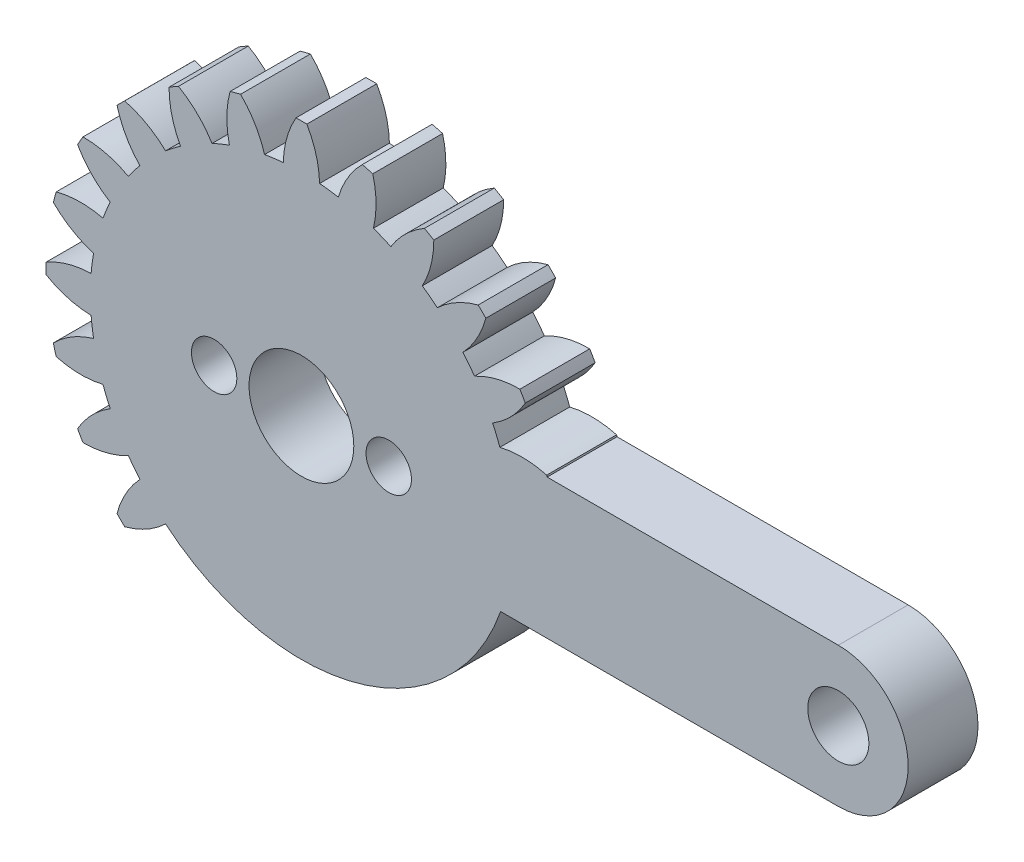
SolidWorks part; units mm, degrees
ref_plane "Front Plane" through (0, 0, 0) normal (0, 0, 1) x (1, 0, 0)
ref_plane "Top Plane" through (0, 0, 0) normal (0, 1, 0) x (1, 0, 0)
ref_plane "Right Plane" through (0, 0, 0) normal (1, 0, 0) x (0, 0, -1)
sketch "Sketch1" plane through (0, 0, 0) normal (0, 0, 1) x (1, 0, 0)
  line L0 (0, 0) -> (0, 14.63) construction
  line L1 (0, 0) -> (30.75, 0) construction
  line L3 (30.75, 4) -> (11.4091, 4)
  line L4 (30.75, -4) -> (11.4091, -4)
  circle A0 centre (0, 0) radius 14.63
  circle A1 centre (0, 0) radius 12.09
  circle A2 centre (0, 0) radius 3
  arc A3 (0.31, 14.6267) -> (1.04, 12.0452) centre (-4.3584, 11.9126) cw
  arc A4 (-0.31, 14.6267) -> (-1.04, 12.0452) centre (4.3584, 11.9126) ccw
  arc A5 (4.0851, 14.0481) -> (4.1221, 11.3656) centre (-1.1267, 12.6347) cw
  arc A6 (3.4862, 14.2086) -> (2.113, 11.9039) centre (7.2931, 10.3787) ccw
  arc A7 (7.5818, 12.5121) -> (6.9233, 9.9114) centre (2.1819, 12.4958) cw
  arc A8 (7.0449, 12.8221) -> (5.1219, 10.9514) centre (9.7308, 8.1374) ccw
  arc A9 (10.5619, 10.1234) -> (9.2526, 7.7818) centre (5.3417, 11.5053) cw
  arc A10 (10.1234, 10.5619) -> (7.7818, 9.2526) centre (11.5053, 5.3417) ccw
  arc A11 (12.8221, 7.0449) -> (10.9514, 5.1219) centre (8.1374, 9.7308) cw
  arc A12 (12.5121, 7.5818) -> (9.9114, 6.9233) centre (12.4958, 2.1819) ccw
  arc A13 (14.2086, 3.4862) -> (11.9039, 2.113) centre (10.3787, 7.2931) cw
  arc A14 (14.0481, 4.0851) -> (11.3656, 4.1221) centre (12.6347, -1.1267) ccw
  arc A15 (14.6267, -0.31) -> (12.0452, -1.04) centre (11.9126, 4.3584) cw
  arc A16 (14.6267, 0.31) -> (12.0452, 1.04) centre (11.9126, -4.3584) ccw
  arc A17 (14.0481, -4.0851) -> (11.3656, -4.1221) centre (12.6347, 1.1267) cw
  arc A18 (14.2086, -3.4862) -> (11.9039, -2.113) centre (10.3787, -7.2931) ccw
  arc A19 (12.5121, -7.5818) -> (9.9114, -6.9233) centre (12.4958, -2.1819) cw
  arc A20 (12.8221, -7.0449) -> (10.9514, -5.1219) centre (8.1374, -9.7308) ccw
  arc A21 (10.1234, -10.5619) -> (7.7818, -9.2526) centre (11.5053, -5.3417) cw
  arc A22 (10.5619, -10.1234) -> (9.2526, -7.7818) centre (5.3417, -11.5053) ccw
  arc A23 (7.0449, -12.8221) -> (5.1219, -10.9514) centre (9.7308, -8.1374) cw
  arc A24 (7.5818, -12.5121) -> (6.9233, -9.9114) centre (2.1819, -12.4958) ccw
  arc A25 (3.4862, -14.2086) -> (2.113, -11.9039) centre (7.2931, -10.3787) cw
  arc A26 (4.0851, -14.0481) -> (4.1221, -11.3656) centre (-1.1267, -12.6347) ccw
  arc A27 (-0.31, -14.6267) -> (-1.04, -12.0452) centre (4.3584, -11.9126) cw
  arc A28 (0.31, -14.6267) -> (1.04, -12.0452) centre (-4.3584, -11.9126) ccw
  arc A29 (-4.0851, -14.0481) -> (-4.1221, -11.3656) centre (1.1267, -12.6347) cw
  arc A30 (-3.4862, -14.2086) -> (-2.113, -11.9039) centre (-7.2931, -10.3787) ccw
  arc A31 (-7.5818, -12.5121) -> (-6.9233, -9.9114) centre (-2.1819, -12.4958) cw
  arc A32 (-7.0449, -12.8221) -> (-5.1219, -10.9514) centre (-9.7308, -8.1374) ccw
  arc A33 (-10.5619, -10.1234) -> (-9.2526, -7.7818) centre (-5.3417, -11.5053) cw
  arc A34 (-10.1234, -10.5619) -> (-7.7818, -9.2526) centre (-11.5053, -5.3417) ccw
  arc A35 (-12.8221, -7.0449) -> (-10.9514, -5.1219) centre (-8.1374, -9.7308) cw
  arc A36 (-12.5121, -7.5818) -> (-9.9114, -6.9233) centre (-12.4958, -2.1819) ccw
  arc A37 (-14.2086, -3.4862) -> (-11.9039, -2.113) centre (-10.3787, -7.2931) cw
  arc A38 (-14.0481, -4.0851) -> (-11.3656, -4.1221) centre (-12.6347, 1.1267) ccw
  arc A39 (-14.6267, 0.31) -> (-12.0452, 1.04) centre (-11.9126, -4.3584) cw
  arc A40 (-14.6267, -0.31) -> (-12.0452, -1.04) centre (-11.9126, 4.3584) ccw
  arc A41 (-14.0481, 4.0851) -> (-11.3656, 4.1221) centre (-12.6347, -1.1267) cw
  arc A42 (-14.2086, 3.4862) -> (-11.9039, 2.113) centre (-10.3787, 7.2931) ccw
  arc A43 (-12.5121, 7.5818) -> (-9.9114, 6.9233) centre (-12.4958, 2.1819) cw
  arc A44 (-12.8221, 7.0449) -> (-10.9514, 5.1219) centre (-8.1374, 9.7308) ccw
  arc A45 (-10.1234, 10.5619) -> (-7.7818, 9.2526) centre (-11.5053, 5.3417) cw
  arc A46 (-10.5619, 10.1234) -> (-9.2526, 7.7818) centre (-5.3417, 11.5053) ccw
  arc A47 (-7.0449, 12.8221) -> (-5.1219, 10.9514) centre (-9.7308, 8.1374) cw
  arc A48 (-7.5818, 12.5121) -> (-6.9233, 9.9114) centre (-2.1819, 12.4958) ccw
  arc A49 (-3.4862, 14.2086) -> (-2.113, 11.9039) centre (-7.2931, 10.3787) cw
  arc A50 (-4.0851, 14.0481) -> (-4.1221, 11.3656) centre (1.1267, 12.6347) ccw
  arc A51 (30.75, 4) -> (30.75, -4) centre (30.75, 0) cw
  circle A52 centre (30.75, 0) radius 1.75
  point P152 (0, 0)
  dimension "D1" = 6
  dimension "D2" = 24.18
  dimension "D3" = 29.26
  dimension "D6" = 5.4
  dimension "D10" = 4
  dimension "D11" = 3.5
  dimension "D4" = 0.62
  dimension "D5" = 2.08
  dimension "D8" = 30.75
  dimension "D9" = 4
  dimension "D12" = 1.0822
  dimension "D7" = 24
extrude "Boss-Extrude3" add sketch "Sketch1" along normal blind 4 contours A1 | A51 L3 A0 L4 A52 | A13 A0 L3 A1 | A16 A0 A13 A1 | A0 A16 A1 A15 | A18 A0 A15 A1 | A0 A18 A1 L4 | A0 A14 A1 L3 | A0 A12 A1 A11 | A0 A10 A1 A9 | A0 A8 A1 A7 | A0 A6 A1 A5 | A0 A4 A1 A3 | A0 A50 A1 A49 | A0 A48 A1 A47 | A0 A46 A1 A45 | A0 A44 A1 A43 | A0 A42 A1 A41 | A0 A40 A1 A39 | A0 A38 A1 A37 | A0 A36 A1 A35 | A0 A34 A1 A33
sketch "Sketch7" plane through (0, 0, 4) normal (0, 0, 1) x (1, 0, 0)
  line L0 (-5, 0) -> (5, 0) construction
  circle A0 centre (5, 0) radius 1.3
  circle A1 centre (-5, 0) radius 1.3
  point P6 (0, 0)
  dimension "D1" = 2.6
  dimension "D3" = 10
extrude "Cut-Extrude1" cut sketch "Sketch7" against normal through all
